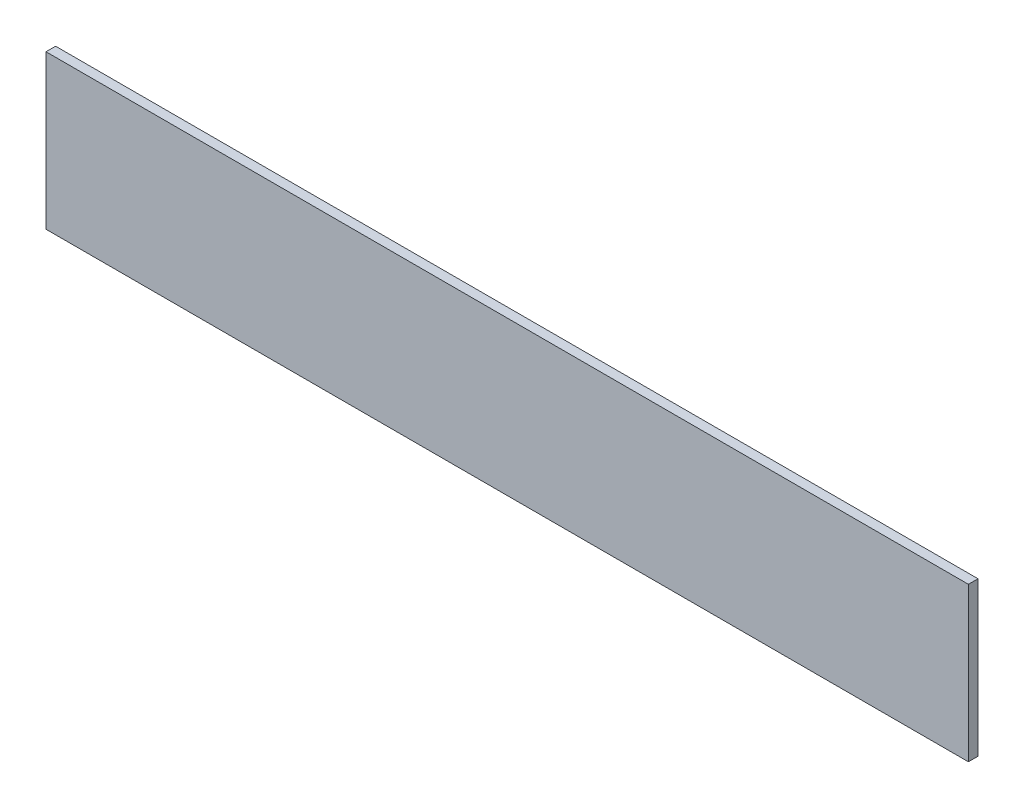
SolidWorks part; units mm, degrees
ref_plane "Front Plane" through (0, 0, 0) normal (0, 0, 1) x (1, 0, 0)
ref_plane "Top Plane" through (0, 0, 0) normal (0, 1, 0) x (1, 0, 0)
ref_plane "Right Plane" through (0, 0, 0) normal (1, 0, 0) x (0, 0, -1)
sketch "Sketch1" plane through (0, 0, 0) normal (0, 0, 1) x (1, 0, 0)
  line L1 (-152.4, -25.4) -> (152.4, -25.4)
  line L2 (-152.4, -25.4) -> (-152.4, 25.4)
  line L3 (-152.4, 25.4) -> (152.4, 25.4)
  line L4 (152.4, -25.4) -> (152.4, 25.4)
  line L5 (-152.4, -25.4) -> (152.4, 25.4) construction
  line L6 (-152.4, 25.4) -> (152.4, -25.4) construction
  point P0 (0, 0)
  dimension "D1" = 50.8
  dimension "D2" = 304.8
extrude "Boss-Extrude1" add sketch "Sketch1" along normal blind 3.175
